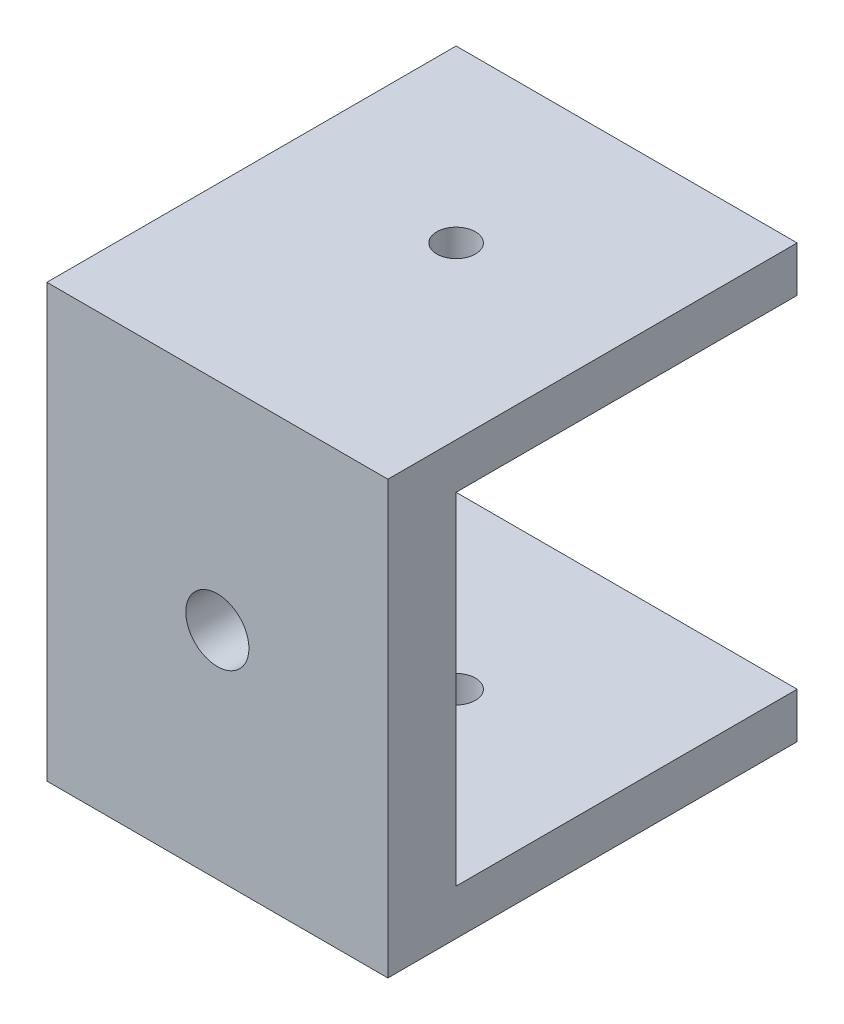
SolidWorks part; units mm, degrees
ref_plane "Front Plane" through (0, 0, 0) normal (0, 0, 1) x (1, 0, 0)
ref_plane "Top Plane" through (0, 0, 0) normal (0, 1, 0) x (1, 0, 0)
ref_plane "Right Plane" through (0, 0, 0) normal (1, 0, 0) x (0, 0, -1)
sketch "Sketch2" plane through (0, 0, 0) normal (1, 0, 0) x (0, 0, -1)
  line L1 (-3, 15) -> (3, 15)
  line L2 (-3, 15) -> (-3, -15)
  line L3 (-3, -15) -> (3, -15)
  line L4 (3, 15) -> (3, -15)
  line L5 (-3, 15) -> (3, -15) construction
  line L6 (-3, -15) -> (3, 15) construction
  line L7 (-3, -15) -> (33, -15)
  line L8 (-3, -15) -> (-3, -19)
  line L9 (-3, -19) -> (33, -19)
  line L10 (33, -15) -> (33, -19)
  line L11 (-3, 15) -> (33, 15)
  line L12 (-3, 15) -> (-3, 19)
  line L13 (-3, 19) -> (33, 19)
  line L14 (33, 15) -> (33, 19)
  point P0 (0, 0)
extrude "Boss-Extrude1" add sketch "Sketch2" along normal blind 30 contours L4 L1 L2 L3 | L11 L14 L13 L12 L1 | L10 L7 L3 L8 L9
sketch "Sketch4" plane through (0, 0, 3) normal (0, 0, 1) x (1, 0, 0)
  line L0 (0, 0) -> (30, 0) construction
  line L1 (0, 19) -> (0, -19) construction
  line L2 (30, 19) -> (30, -19) construction
  circle A0 centre (15, 0) radius 2.775
  dimension "D1" = 5.55
extrude "Cut-Extrude2" cut sketch "Sketch4" against normal blind 30
sketch "Sketch5" plane through (0, -19, 0) normal (0, -1, 0) x (1, 0, 0)
  line L0 (15, -33) -> (15, -18) construction
  line L1 (30, -33) -> (0, -33) construction
  circle A0 centre (15, -18) radius 1.7
extrude "Cut-Extrude3" cut sketch "Sketch5" against normal through all
